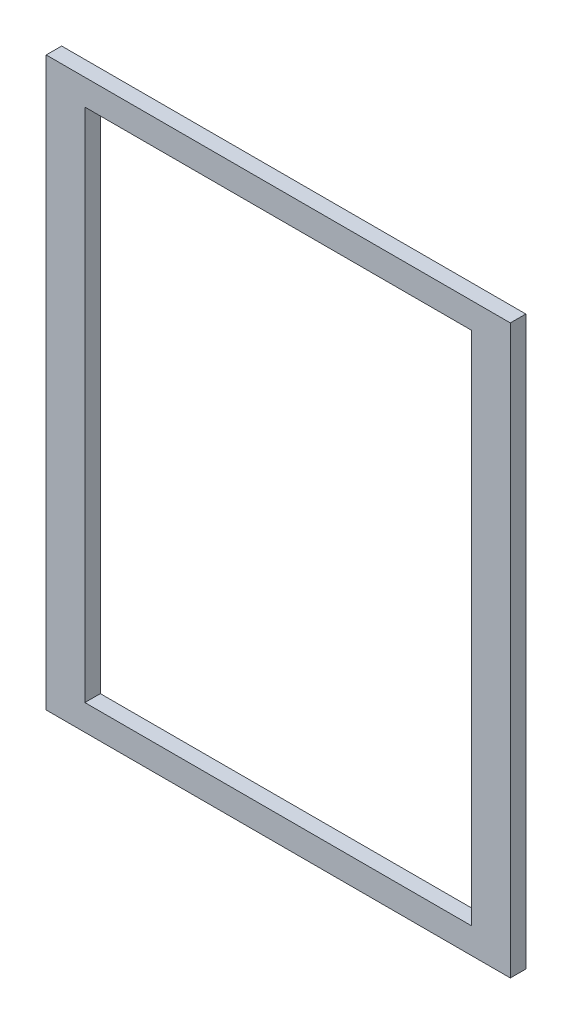
SolidWorks part; units mm, degrees
material "Birch plywood FK"
ref_plane "Спереди" through (0, 0, 0) normal (0, 0, 1) x (1, 0, 0)
ref_plane "Сверху" through (0, 0, 0) normal (0, 1, 0) x (1, 0, 0)
ref_plane "Справа" through (0, 0, 0) normal (1, 0, 0) x (0, 0, -1)
sketch "Эскиз1" plane through (0, 0, 0) normal (0, 0, 1) x (1, 0, 0)
  line L1 (75, -100) -> (-75, -100)
  line L2 (75, -100) -> (75, 100)
  line L3 (75, 100) -> (-75, 100)
  line L4 (-75, -100) -> (-75, 100)
  line L5 (75, -100) -> (-75, 100) construction
  line L6 (75, 100) -> (-75, -100) construction
  line L7 (90, -110) -> (-90, -110)
  line L8 (90, -110) -> (90, 110)
  line L9 (90, 110) -> (-90, 110)
  line L10 (-90, -110) -> (-90, 110)
  line L11 (90, -110) -> (-90, 110) construction
  line L12 (90, 110) -> (-90, -110) construction
  point P0 (0, 0)
  point P6 (0, 0)
  dimension "D1" = 150
  dimension "D2" = 200
  dimension "D3" = 220
  dimension "D4" = 15
extrude "Бобышка-Вытянуть1" add sketch "Эскиз1" along normal blind 6
